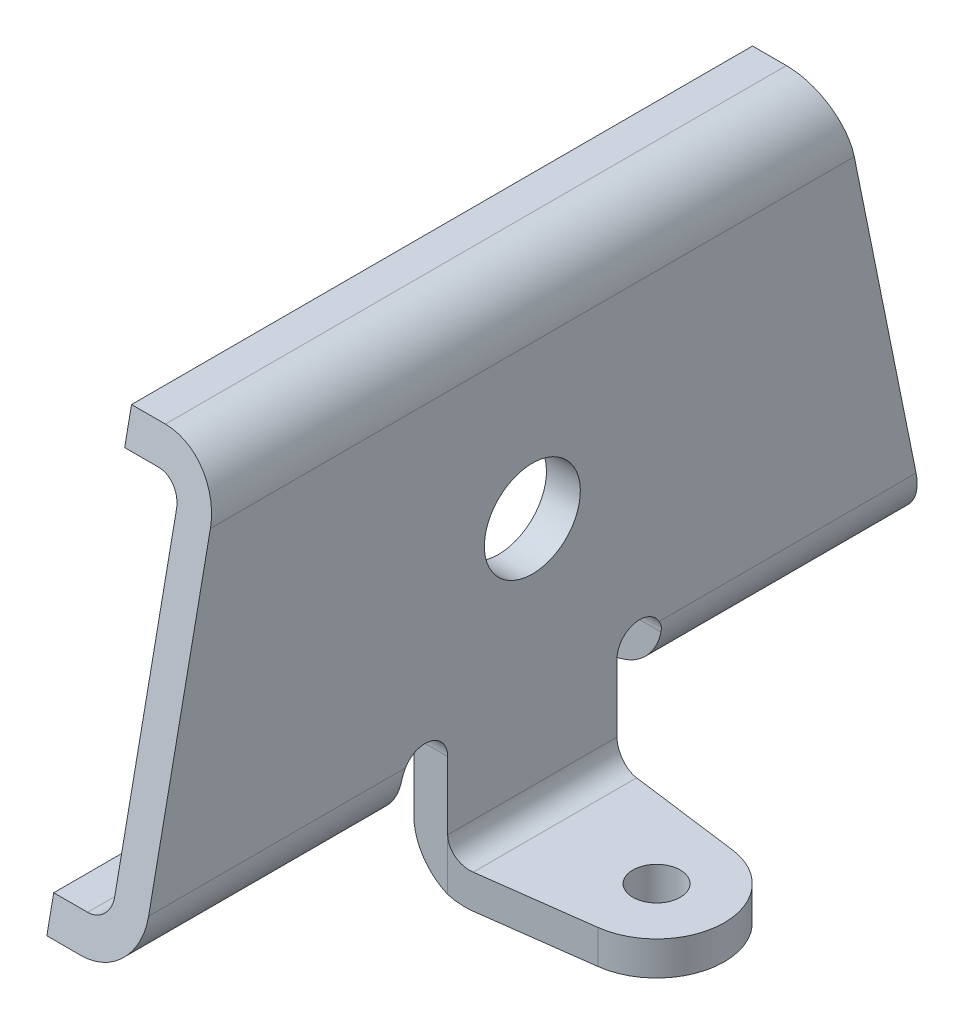
SolidWorks part; units mm, degrees
ref_plane "Plan de face" through (0, 0, 0) normal (0, 0, 1) x (1, 0, 0)
ref_plane "Plan de dessus" through (0, 0, 0) normal (0, 1, 0) x (1, 0, 0)
ref_plane "Plan de droite" through (0, 0, 0) normal (1, 0, 0) x (0, 0, -1)
sketch "Esquisse1" plane through (0, 0, 0) normal (0, 0, 1) x (1, 0, 0)
  line L0 (0, 0) -> (-16.6258, 0) construction
  line L1 (-3, -25.5) -> (17, -25.5) construction
  line L13 (-8, 18.5) -> (0, 18.5)
  line L14 (0, 18.5) -> (0, -25.5)
  line L16 (-3, -18.5) -> (-8, -18.5)
  line L17 (-3, -15.5) -> (-8, -15.5)
  line L18 (-3, 15.5) -> (-3, -15.5)
  line L19 (-3, -25.5) -> (0, -25.5)
  line L20 (-8, 15.5) -> (-3, 15.5)
  line L21 (-8, 18.5) -> (-8, 15.5)
  line L22 (-8, -15.5) -> (-8, -18.5)
  line L24 (-2.5688, -15.5) -> (-8, -15.5) construction
  line L25 (-2.5688, -18.5) -> (-8, -18.5) construction
  line L26 (-3, -18.5) -> (-3, -25.5)
  line L27 (-3, 2.9186) -> (-3, -25.5) construction
  line L28 (-8, 15.5) -> (0, 15.5) construction
  line L29 (0, 2.9186) -> (0, -22.5) construction
  line L30 (0, -22.5) -> (17, -22.5) construction
  dimension "D8" = 44
  dimension "D9" = 31
  dimension "D11" = 8
  dimension "D7" = 3
extrude "Extrusion1" add sketch "Esquisse1" along normal mid plane 70
sketch "Esquisse2" plane through (-8, 0, 0) normal (-1, 0, 0) x (0, 0, 1)
  line L0 (0, 0) -> (0, -28.9888) construction
  line L2 (35, -25.5) -> (-35, -25.5) construction
  line L3 (-11.4976, -25.5) -> (-11.4976, -14.4988)
  line L4 (7.5, -25.5) -> (7.5, -14.4988)
  line L5 (-7.5, -25.5) -> (-7.5, -14.4988)
  line L6 (11.4976, -25.5) -> (11.4976, -14.4988)
  line L7 (35, 18.5) -> (-35, 18.5) construction
  line L8 (-11.4976, -25.5) -> (-7.5, -25.5)
  line L10 (7.5, -25.5) -> (11.4976, -25.5)
  arc A0 (-7.5, -14.4988) -> (-11.4976, -14.4988) centre (-9.4988, -14.4988) ccw
  arc A1 (7.5, -14.4988) -> (11.4976, -14.4988) centre (9.4988, -14.4988) cw
  dimension "D3" = 31
  dimension "D1" = 3.9976
  dimension "D2" = 15
extrude "Enlèv. mat.-Extru.1" cut sketch "Esquisse2" against normal through all
sketch "Esquisse8" plane through (-3, 0, 0) normal (-1, 0, 0) x (0, 0, 1)
  line L1 (-7.5, -18.5) -> (7.5, -18.5)
  line L2 (-7.5, -18.5) -> (-7.5, -15.5)
  line L3 (-7.5, -15.5) -> (7.5, -15.5)
  line L4 (7.5, -18.5) -> (7.5, -15.5)
extrude "Enlèv. mat.-Extru.8" cut sketch "Esquisse8" along normal through all
sketch "Esquisse9" plane through (-3, 0, 0) normal (-1, 0, 0) x (0, 0, 1)
  line L1 (-11.4976, -18.5) -> (-35, -18.5)
  line L2 (-11.4976, -18.5) -> (-11.4976, -25.5)
  line L3 (-11.4976, -25.5) -> (-35, -25.5)
  line L4 (-35, -18.5) -> (-35, -25.5)
  line L5 (35, -18.5) -> (11.4976, -18.5)
  line L6 (35, -18.5) -> (35, -25.5)
  line L7 (35, -25.5) -> (11.4976, -25.5)
  line L8 (11.4976, -18.5) -> (11.4976, -25.5)
extrude "Enlèv. mat.-Extru.9" cut sketch "Esquisse9" against normal through all
sketch "Esquisse11" plane through (0, -25.5, 0) normal (0, -1, 0) x (1, 0, 0)
  line L0 (0, 7.5) -> (11.7832, 5.9487)
  line L1 (0, -7.5) -> (11.7832, -5.9487)
  line L2 (-3, 7.5) -> (-3, -7.5) construction
  line L3 (0, 7.5) -> (0, -7.5)
  arc A0 (11.7832, -5.9487) -> (11.7832, 5.9487) centre (11, 0) ccw
  circle A1 centre (11, 0) radius 2.1
  dimension "D2" = 6
  dimension "D3" = 4.2
  dimension "D1" = 14
extrude "Extrusion2" add sketch "Esquisse11" against normal blind 3
sketch "Esquisse12" plane through (-3, 0, 0) normal (-1, 0, 0) x (0, 0, 1)
  circle A0 centre (0, 0) radius 4.25
  dimension "D1" = 8.5
extrude "Enlèv. mat.-Extru.10" cut sketch "Esquisse12" against normal through all
fillet "Congé3" radius 2 8 edges at (-3, -15.5, 23.2488) (-3, 15.5, 0) (-3, -15.5, -23.2488) (-3, -14.9994, -11.4976) (-3, -14.9994, 11.4976)
fillet "Congé4" radius 5 9 edges at (0, -18.5, -23.2488) (0, -16.4994, 11.4976) (0, -18.5, 23.2488) (0, 18.5, 0) (-1.5, -25.5, -7.5) (0, -16.4994, -11.4976) (-3, -25.5, 0) (-1.5, -25.5, 7.5)
sketch "Esquisse13" plane through (0, 0, 0) normal (1, 0, 0) x (0, 0, -1)
  line L0 (0, 0) -> (0, 20.9591) construction
  line L1 (-35, 18.5) -> (-35, -18.5)
  line L2 (-35, -18.5) -> (-27.5, 18.5)
  line L3 (-35, 18.5) -> (35, 18.5) construction
  line L4 (-27.5, 18.5) -> (-35, 18.5)
  line L5 (35, 18.5) -> (35, -18.5)
  line L6 (27.5, 18.5) -> (35, 18.5)
  line L7 (35, -18.5) -> (27.5, 18.5)
  dimension "D1" = 55
extrude "Enlèv. mat.-Extru.11" cut sketch "Esquisse13" against normal through all
